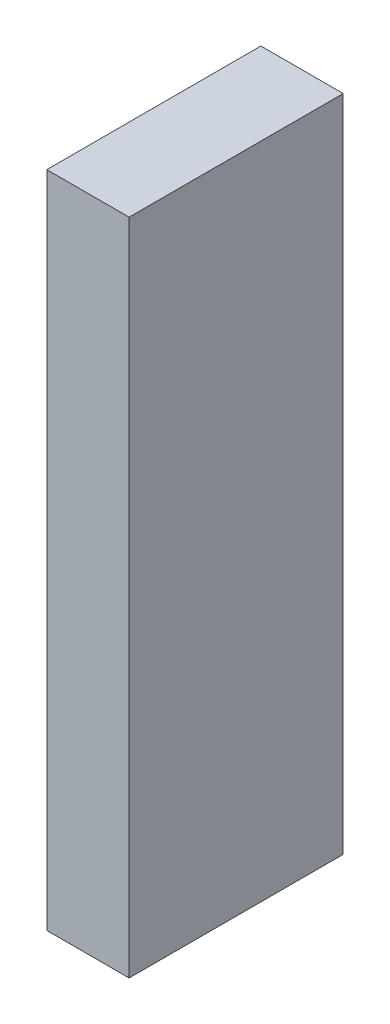
SolidWorks part; units mm, degrees
material "POLYURETHANE (11671)"
ref_plane "Front Plane" through (0, 0, 0) normal (0, 0, 1) x (1, 0, 0)
ref_plane "Top Plane" through (0, 0, 0) normal (0, 1, 0) x (1, 0, 0)
ref_plane "Right Plane" through (0, 0, 0) normal (1, 0, 0) x (0, 0, -1)
sketch "Sketch1" plane through (0, 0, 0) normal (1, 0, 0) x (0, 0, -1)
  line L1 (-4.1275, -12.7) -> (4.1275, -12.7)
  line L2 (-4.1275, -12.7) -> (-4.1275, 12.7)
  line L3 (-4.1275, 12.7) -> (4.1275, 12.7)
  line L4 (4.1275, -12.7) -> (4.1275, 12.7)
  line L5 (-4.1275, -12.7) -> (4.1275, 12.7) construction
  line L6 (-4.1275, 12.7) -> (4.1275, -12.7) construction
  point P0 (0, 0)
  dimension "D1" = 8.255
  dimension "D2" = 25.4
extrude "Boss-Extrude1" add sketch "Sketch1" along normal blind 3.175
